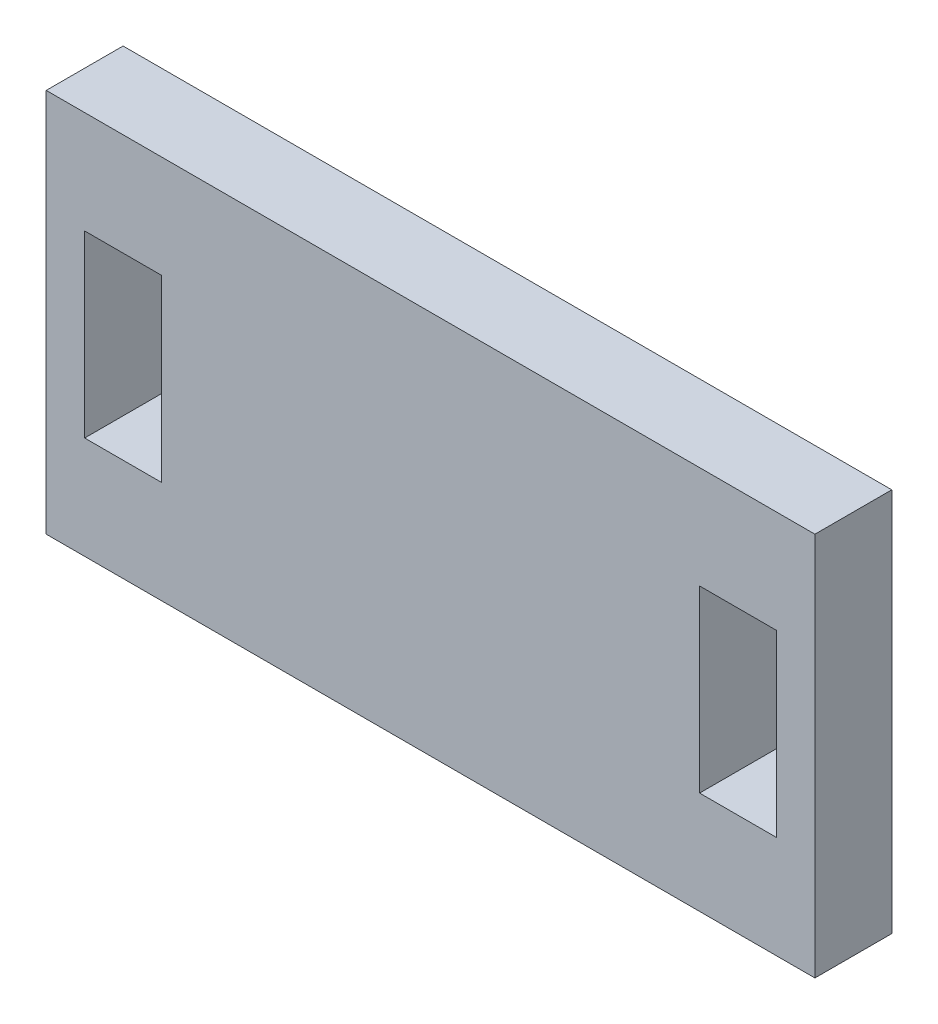
SolidWorks part; units mm, degrees
ref_plane "Front Plane" through (0, 0, 0) normal (0, 0, 1) x (1, 0, 0)
ref_plane "Top Plane" through (0, 0, 0) normal (0, 1, 0) x (1, 0, 0)
ref_plane "Right Plane" through (0, 0, 0) normal (1, 0, 0) x (0, 0, -1)
sketch "Sketch1" plane through (0, 0, 0) normal (0, 0, 1) x (1, 0, 0)
  line L1 (-15, 7.5) -> (15, 7.5)
  line L2 (-15, 7.5) -> (-15, -7.5)
  line L3 (-15, -7.5) -> (15, -7.5)
  line L4 (15, 7.5) -> (15, -7.5)
  line L5 (-15, 7.5) -> (15, -7.5) construction
  line L6 (-15, -7.5) -> (15, 7.5) construction
  line L7 (-13.5, 3.5) -> (-10.5, 3.5)
  line L8 (-13.5, 3.5) -> (-13.5, -3.5)
  line L9 (-13.5, -3.5) -> (-10.5, -3.5)
  line L10 (-10.5, 3.5) -> (-10.5, -3.5)
  line L11 (10.5, 3.5) -> (13.5, 3.5)
  line L12 (10.5, 3.5) -> (10.5, -3.5)
  line L13 (10.5, -3.5) -> (13.5, -3.5)
  line L14 (13.5, 3.5) -> (13.5, -3.5)
  point P0 (0, 0)
  dimension "D1" = 30
  dimension "D2" = 15
  dimension "D3" = 1.5
  dimension "D4" = 4
  dimension "D5" = 4
  dimension "D6" = 4.5
  dimension "D7" = 4.5
  dimension "D8" = 1.5
  dimension "D9" = 4
  dimension "D10" = 4
extrude "Boss-Extrude1" add sketch "Sketch1" along normal mid plane 3
